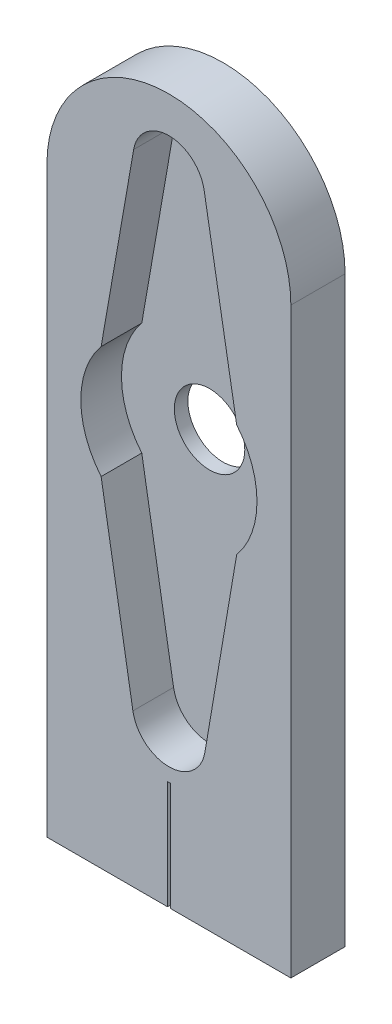
SolidWorks part; units mm, degrees
ref_plane "前基準面" through (0, 0, 0) normal (0, 0, 1) x (1, 0, 0)
ref_plane "上基準面" through (0, 0, 0) normal (0, 1, 0) x (1, 0, 0)
ref_plane "右基準面" through (0, 0, 0) normal (1, 0, 0) x (0, 0, -1)
sketch "草圖1" plane through (0, 0, 0) normal (0, 0, 1) x (1, 0, 0)
  line L0 (-9, 0) -> (-9, 43)
  line L1 (0, 45.5769) -> (0, 0) construction
  line L2 (-9, 0) -> (9, 0)
  line L3 (9, 0) -> (9, 43)
  arc A0 (-9, 43) -> (9, 43) centre (0, 43) cw
  dimension "D1" = 18
  dimension "D2" = 43
extrude "填料-伸長1" add sketch "草圖1" along normal blind 4 contours L3 A0 L0 L2
sketch "草圖2" plane through (0, 0, 4) normal (0, 0, 1) x (1, 0, 0)
  line L0 (-2.6, 47.1451) -> (-5, 33.3524)
  line L1 (2.6, 47.1451) -> (5, 33.3524)
  line L2 (-5, 25.0457) -> (-2.6563, 11.2433)
  line L3 (5, 25.0457) -> (2.6563, 11.2433)
  line L4 (-9, 0) -> (9, 0) construction
  line L5 (0, 0) -> (0, 9) construction
  line L6 (0, 49.3318) -> (0, 46.5984) construction
  line L7 (0, 15.3887) -> (0, 39.6759) construction
  arc A0 (-2.6563, 11.2433) -> (2.6563, 11.2433) centre (0, 11.6943) ccw
  arc A1 (2.6, 47.1451) -> (-2.6, 47.1451) centre (0, 46.6927) ccw
  arc A2 (5, 25.0457) -> (5, 33.3524) centre (0, 29.199) ccw
  arc A3 (-5, 33.3524) -> (-5, 25.0457) centre (0, 29.199) ccw
  point P19 (0, 0)
  dimension "D1" = 9
  dimension "D2" = 13
  dimension "D4" = 2.6
  dimension "D3" = 14
  dimension "D5" = 5
  dimension "D6" = 5
extrude "除料-伸長1" cut sketch "草圖2" against normal blind 3 contours L3 A0 L2 A3 L0 A1 L1 A2
sketch "草圖4" plane through (0, 0, 0) normal (0, 0, 1) x (1, 0, 0)
  line L0 (-9, 29.0652) -> (9, 29.0652) construction
  line L1 (-9, 0) -> (-9, 43) construction
  line L2 (9, 0) -> (9, 43) construction
  line L3 (0, 0) -> (0, 52) construction
  arc A0 (9, 43) -> (-9, 43) centre (0, 43) ccw construction
  circle A1 centre (0, 29.0652) radius 2.6
  dimension "D1" = 5.2
extrude "除料-伸長9" cut sketch "草圖4" against normal blind 2 and the other way blind 19
sketch "草圖5" plane through (0, 0, 0) normal (0, 0, 1) x (1, 0, 0)
  line L0 (0, 0) -> (0, 9) construction
  line L1 (-9, 0) -> (9, 0) construction
  line L11 (-0.1, 0) -> (0.1, 0)
  line L12 (-0.1, 0) -> (-0.1, 8)
  line L13 (-0.1, 8) -> (0.1, 8)
  line L14 (0.1, 0) -> (0.1, 8)
  arc A0 (-2.6563, 11.2433) -> (2.6563, 11.2433) centre (0, 11.6943) ccw construction
  point P12 (0, 7.9974)
  dimension "D1" = 0.2
  dimension "D2" = 8
extrude "除料-伸長11" cut sketch "草圖5" along normal through all contours L12 L13 L14 L11
